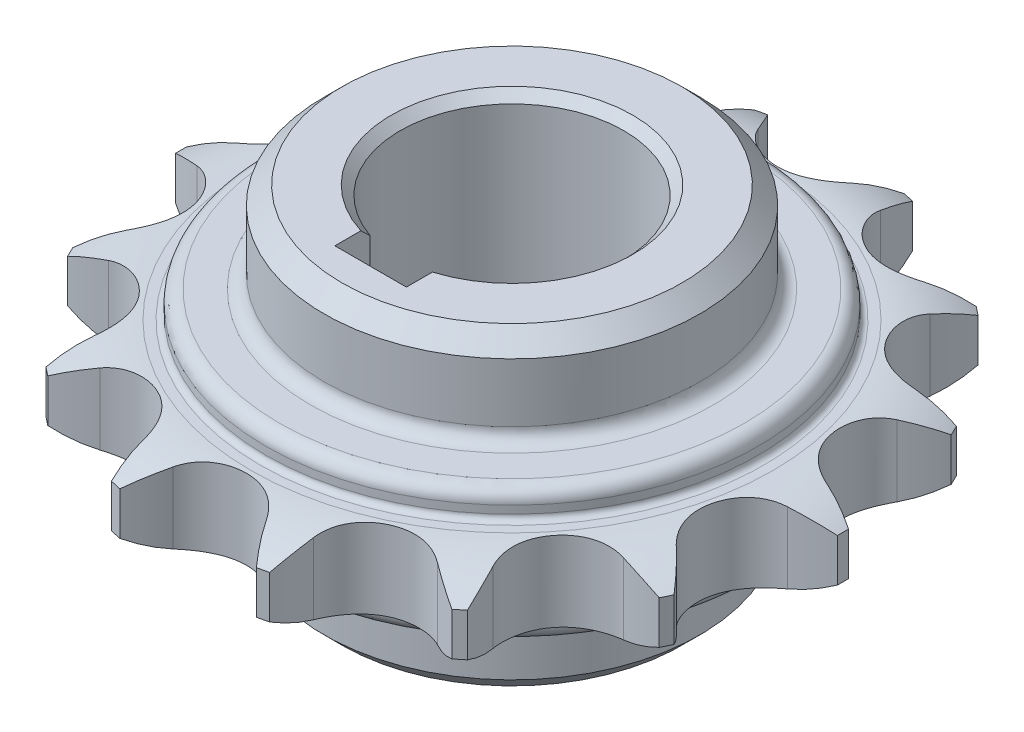
SolidWorks part; units mm, degrees
material "AISI 1045 钢，冷拔"
ref_plane "前视基准面" through (0, 0, 0) normal (0, 0, 1) x (1, 0, 0)
ref_plane "上视基准面" through (0, 0, 0) normal (0, 1, 0) x (1, 0, 0)
ref_plane "右视基准面" through (0, 0, 0) normal (1, 0, 0) x (0, 0, -1)
sketch "草图1" plane through (0, 0, 0) normal (0, 1, 0) x (1, 0, 0)
  line L0 (0, 0) -> (0, 51.7486) construction
  line L1 (0, 0) -> (25.3679, 52.6769) construction
  line L2 (0, 35.6709) -> (32.0589, 17.1616) construction
  line L3 (15.477, 32.1383) -> (-15.3885, 29.8253) construction
  line L4 (0, 29.6709) -> (0, 0)
  line L5 (0, 0) -> (12.8737, 26.7325)
  circle A0 centre (0, 0) radius 35.6709 construction
  arc A1 (0, 29.6709) -> (5.1962, 32.6708) centre (0, 35.6709) ccw
  arc A2 (9.4938, 31.6899) -> (12.8737, 26.7325) centre (15.477, 32.1383) ccw
  arc A3 (8.8341, 35.9299) -> (7.6301, 36.2047) centre (0, 0) ccw
  arc A4 (7.6301, 36.2047) -> (5.1962, 32.6708) centre (28.5788, 19.1708) ccw
  arc A5 (9.4938, 31.6899) -> (8.8341, 35.9299) centre (-17.4307, 29.6722) ccw
  point P150 (0, 0)
  dimension "D1" = 71.3417
  dimension "D3" = 12
  dimension "D4" = 12
  dimension "D5" = 74
  dimension "D8" = 54
  dimension "D9" = 54
  dimension "D2" = 25.714
  dimension "D6" = 60
  dimension "D7" = 60
extrude "凸台-拉伸1" add sketch "草图1" along normal blind 8.93
pattern_circular "阵列(圆周)1" count 14 over 360 about axis through (0, 0, 0) along (0, 1, 0) of "凸台-拉伸1"
sketch "草图2" plane through (0, 0, 0) normal (0, 0, 1) x (1, 0, 0)
  line L0 (36.9948, 4.465) -> (-36.9948, 4.465) construction
  line L1 (36.9948, 8.93) -> (36.9948, 0) construction
  line L2 (-36.9948, 8.93) -> (-36.9948, 0) construction
  line L3 (39.2107, 6.8663) -> (27.425, 6.8662) construction
  line L4 (39.2107, 2.0638) -> (27.425, 2.0637) construction
  line L5 (33.008, 0) -> (36.9948, 0) construction
  line L6 (36.9948, 8.93) -> (33.008, 8.93) construction
  line L7 (28.7828, 8.93) -> (21.8886, 8.93) construction
  line L8 (36.9948, 8.93) -> (36.9948, 0) construction
  line L9 (36.9948, 8.93) -> (29.1677, 8.93)
  line L10 (21.8886, 0) -> (28.7828, 0) construction
  line L13 (36.9948, 0) -> (29.1677, 0)
  line L14 (36.9948, 6.8663) -> (36.9948, 2.0637)
  line L15 (36.9948, 8.93) -> (43.7467, 8.93)
  line L16 (43.7467, 8.93) -> (43.7467, 0)
  line L17 (43.7467, 0) -> (36.9948, 0)
  line L18 (0, 0) -> (0, 52.4922) construction
  arc A0 (36.9948, 6.8663) -> (29.1677, 8.93) centre (29.1677, -6.945) ccw
  arc A1 (29.1677, 0) -> (36.9948, 2.0637) centre (29.1677, 15.875) ccw
  point P22 (36.9948, 6.8663)
  point P25 (36.9948, 2.0637)
  dimension "D3" = 31.75
  dimension "D4" = 31.75
  dimension "D1" = 2.0638
  dimension "D2" = 2.0638
revolve "切除-旋转1" cut sketch "草图2" angle 360 about L18
sketch "草图4" plane through (0, 0, 0) normal (0, -1, 0) x (1, 0, 0)
  circle A0 centre (0, 0) radius 27.5
  dimension "D1" = 55
extrude "凸台-拉伸3" add sketch "草图4" along normal blind 3
sketch "草图3" plane through (0, 8.93, 0) normal (0, 1, 0) x (1, 0, 0)
  circle A0 centre (0, 0) radius 27.5
  dimension "D1" = 55
extrude "凸台-拉伸2" add sketch "草图3" along normal blind 3
sketch "草图5" plane through (0, 11.93, 0) normal (0, 1, 0) x (1, 0, 0)
  circle A0 centre (0, 0) radius 21
  dimension "D1" = 42
extrude "凸台-拉伸4" add sketch "草图5" along normal offset from surface (10.07 mm away) 25 up to face at (0, -3, -27.5)
fillet "圆角1" radius 0.635 2 edges at (0, 8.93, 27.5) (0, 0, 27.5)
fillet "圆角2" radius 1.5 3 edges at (0, 11.93, 21) (0, 11.93, 27.5) (0, -3, -27.5)
chamfer "倒角1" distance 2 angle 45 1 edges at (0, 22, -21)
sketch "草图8" plane through (0, -3, 0) normal (0, -1, 0) x (1, 0, 0)
  circle A0 centre (0, 0) radius 21
  dimension "D1" = 42
sketch "草图6" plane through (0, 22, 0) normal (0, 1, 0) x (1, 0, 0)
  circle A0 centre (0, 0) radius 12.5
  dimension "D1" = 25
extrude "切除-拉伸3" cut sketch "草图6" against normal blind 40
sketch "草图7" plane through (0, -3, 0) normal (0, -1, 0) x (1, 0, 0)
  line L0 (0, 0) -> (0, 52.6933) construction
  line L1 (-4, 11.8427) -> (-4, 15.8)
  line L2 (4, 11.8427) -> (4, 15.8)
  line L3 (-4, 15.8) -> (4, 15.8)
  line L5 (-4, 0) -> (-4, 52.6933) construction
  line L6 (4, 0) -> (4, 52.6933) construction
  circle A0 centre (0, 0) radius 12.5 construction
  arc A1 (4, 11.8427) -> (-4, 11.8427) centre (0, 0) ccw
  dimension "D1" = 4
  dimension "D3" = 15.8
  dimension "D2" = 4
extrude "切除-拉伸4" cut sketch "草图7" against normal up to next
sketch "草图9" plane through (0, -3, 0) normal (0, -1, 0) x (1, 0, 0)
  circle A0 centre (0, 0) radius 21 construction
  circle A1 centre (0, 0) radius 21
extrude "凸台-拉伸5" add sketch "草图9" along normal blind 10.07
sketch "草图10" plane through (0, -3, 0) normal (0, 1, 0) x (1, 0, 0)
  line L3 (-4, -15.8) -> (4, -15.8)
  line L4 (4, -15.8) -> (4, -11.8427)
  line L5 (-4, -11.8427) -> (-4, -15.8)
  line L6 (-4, -15.8) -> (4, -15.8)
  line L7 (4, -15.8) -> (4, -11.8427)
  line L8 (-4, -11.8427) -> (-4, -15.8)
  arc A1 (4, -11.8427) -> (-4, -11.8427) centre (0, 0) ccw
  arc A2 (4, -11.8427) -> (-4, -11.8427) centre (0, 0) ccw
  dimension "D1" = 0
extrude "切除-拉伸5" cut sketch "草图10" against normal up to next
chamfer "倒角2" distance 2 angle 45 1 edges at (0, -13.07, -21)
fillet "圆角3" radius 1.5 1 edges at (0, -3, -21)
chamfer "倒角3" distance 1 angle 45 2 edges at (0, 22, -12.5) (0, -13.07, -12.5)
